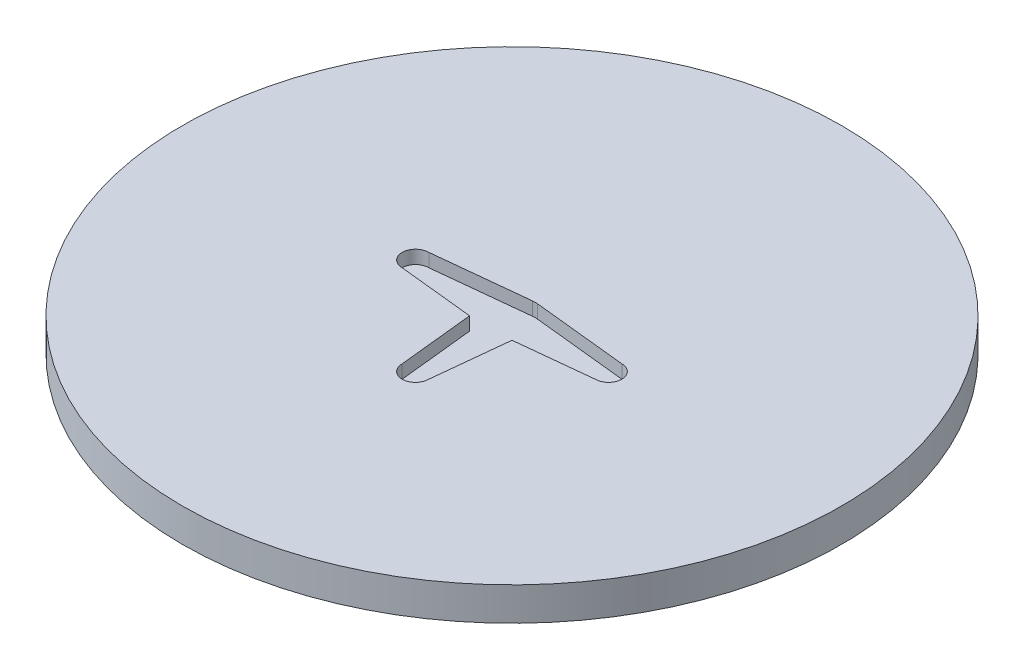
SolidWorks part; units mm, degrees
ref_plane "Front Plane" through (0, 0, 0) normal (0, 0, 1) x (1, 0, 0)
ref_plane "Top Plane" through (0, 0, 0) normal (0, 1, 0) x (1, 0, 0)
ref_plane "Right Plane" through (0, 0, 0) normal (1, 0, 0) x (0, 0, -1)
sketch "Sketch1" plane through (0, 0, 0) normal (0, 1, 0) x (1, 0, 0)
  circle A0 centre (0, 0) radius 49.5
  dimension "D1" = 99
extrude "Boss-Extrude1" add sketch "Sketch1" along normal blind 5
sketch "Sketch2" plane through (0, 5, 0) normal (0, 1, 0) x (1, 0, 0)
  line L1 (14.5, 2) -> (0.3647, 3.4809)
  line L2 (14.5, -2) -> (3.1854, -3.1854)
  line L3 (2, -14.5) -> (3.1854, -3.1854)
  line L4 (-2, -14.5) -> (-3.1854, -3.1854)
  line L5 (-14.5, -2) -> (-3.1854, -3.1854)
  line L6 (-14.5, 2) -> (-0.3647, 3.4809)
  arc A1 (14.5, -2) -> (14.5, 2) centre (14.5, 0) ccw
  arc A9 (-2, -14.5) -> (2, -14.5) centre (0, -14.5) ccw
  arc A10 (-14.5, 2) -> (-14.5, -2) centre (-14.5, 0) ccw
  arc A11 (0.3647, 3.4809) -> (-0.3647, 3.4809) centre (0, 0) ccw
  point P18 (0, 0)
  point P23 (0, 0)
  point P24 (0, 0)
  point P38 (0, 0)
  dimension "D2" = 4
  dimension "D3" = 3
extrude "Cut-Extrude1" cut sketch "Sketch2" against normal blind 2
sketch "Sketch3" plane through (0, 0, 0) normal (0, -1, 0) x (1, 0, 0)
  ellipse E0 centre (0, 0) end of major axis (0, -25) minor radius 7.5 (7.1837, 7.1837) -> (-7.1837, 7.1837) ccw
  ellipse E1 centre (0, 0) end of major axis (-25, 0) minor radius 7.5 (7.1837, -7.1837) -> (7.1837, 7.1837) ccw
  ellipse E2 centre (0, 0) end of major axis (0, -25) minor radius 7.5 (-7.1837, -7.1837) -> (7.1837, -7.1837) ccw
  ellipse E3 centre (0, 0) end of major axis (-25, 0) minor radius 7.5 (-7.1837, 7.1837) -> (-7.1837, -7.1837) ccw
  point P15 (0, 0)
  point P23 (0, 0)
  point P24 (0, 0)
extrude "Cut-Extrude2" cut sketch "Sketch3" against normal blind 2
